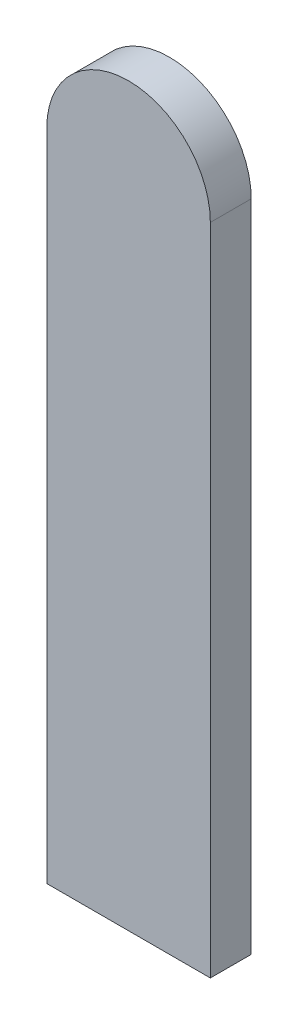
SolidWorks part; units mm, degrees
ref_plane "Front Plane" through (0, 0, 0) normal (0, 0, 1) x (1, 0, 0)
ref_plane "Top Plane" through (0, 0, 0) normal (0, 1, 0) x (1, 0, 0)
ref_plane "Right Plane" through (0, 0, 0) normal (1, 0, 0) x (0, 0, -1)
sketch "Sketch1" plane through (0, 0, 0) normal (0, 0, 1) x (1, 0, 0)
  line L0 (0, 0) -> (-4, 0)
  line L1 (-4, 0) -> (-4, 16)
  line L2 (0, 0) -> (0, 16)
  arc A0 (-4, 16) -> (0, 16) centre (-2, 16) cw
extrude "Boss-Extrude1" add sketch "Sketch1" along normal blind 1
